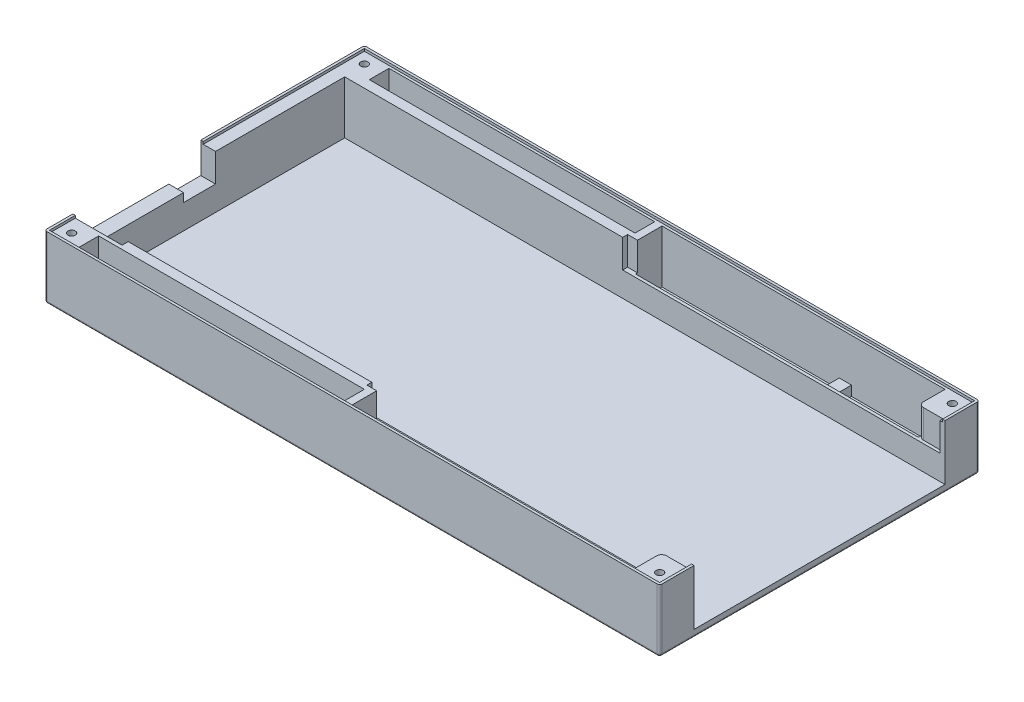
SolidWorks part; units mm, degrees
ref_plane "Front Plane" through (0, 0, 0) normal (0, 0, 1) x (1, 0, 0)
ref_plane "Top Plane" through (0, 0, 0) normal (0, 1, 0) x (1, 0, 0)
ref_plane "Right Plane" through (0, 0, 0) normal (1, 0, 0) x (0, 0, -1)
sketch "Sketch1" plane through (0, 0, 0) normal (0, 1, 0) x (1, 0, 0)
  line L1 (-125, -65) -> (125, -65)
  line L2 (-125, -65) -> (-125, 65)
  line L3 (-125, 65) -> (125, 65)
  line L4 (125, -65) -> (125, 65)
  line L5 (-125, -65) -> (125, 65) construction
  line L6 (-125, 65) -> (125, -65) construction
  point P0 (0, 0)
extrude "Boss-Extrude1" add sketch "Sketch1" along normal blind 3
sketch "Sketch2" plane through (0, 0, 0) normal (0, 1, 0) x (1, 0, 0)
  line L0 (125, -65) -> (125, 65) construction
  line L1 (-125, 65) -> (125, 65)
  line L2 (-125, 65) -> (-125, 64)
  line L3 (-125, 64) -> (125, 64)
  line L4 (125, 65) -> (125, 64)
  dimension "D1" = 1
extrude "Boss-Extrude2" add sketch "Sketch2" along normal blind 25.5
sketch "Sketch3" plane through (0, 3, 0) normal (0, 1, 0) x (1, 0, 0)
  line L0 (125, -65) -> (125, 64) construction
  line L1 (-125, -65) -> (125, -65)
  line L2 (-125, -65) -> (-125, -64)
  line L3 (-125, -64) -> (125, -64)
  line L4 (125, -65) -> (125, -64)
  dimension "D1" = 1
extrude "Boss-Extrude3" add sketch "Sketch3" along normal blind 22.5
sketch "Sketch4" plane through (0, 3, 0) normal (0, 1, 0) x (1, 0, 0)
  line L0 (125, -64) -> (-125, -64) construction
  line L1 (-125, 64) -> (-124, 64)
  line L2 (-125, 64) -> (-125, -64)
  line L3 (-125, -64) -> (-124, -64)
  line L4 (-124, 64) -> (-124, -64)
  dimension "D1" = 1
extrude "Boss-Extrude4" add sketch "Sketch4" along normal blind 22.5
sketch "Sketch6" plane through (0, 3, 0) normal (0, 1, 0) x (1, 0, 0)
  line L1 (125, -65) -> (124, -65)
  line L2 (125, -65) -> (125, -51)
  line L3 (125, -51) -> (124, -51)
  line L4 (124, -65) -> (124, -51)
  dimension "D1" = 1
  dimension "D2" = 14
extrude "Boss-Extrude5" add sketch "Sketch6" along normal blind 22.5
sketch "Sketch7" plane through (0, 3, 0) normal (0, 1, 0) x (1, 0, 0)
  line L1 (125, 65) -> (124, 65)
  line L2 (125, 65) -> (125, 51)
  line L3 (125, 51) -> (124, 51)
  line L4 (124, 65) -> (124, 51)
  dimension "D1" = 1
  dimension "D2" = 14
extrude "Boss-Extrude6" add sketch "Sketch7" along normal blind 22.5
sketch "Sketch8" plane through (0, 3, 0) normal (0, 1, 0) x (1, 0, 0)
  line L0 (-124, 64) -> (124, 64) construction
  line L1 (124, 51) -> (123, 51)
  line L2 (124, 51) -> (124, 64)
  line L3 (124, 64) -> (123, 64)
  line L4 (123, 51) -> (123, 64)
  dimension "D1" = 1
extrude "Boss-Extrude7" add sketch "Sketch8" along normal blind 21.5
sketch "Sketch10" plane through (0, 3, 0) normal (0, 1, 0) x (1, 0, 0)
  line L0 (-124, -64) -> (-124, 64) construction
  line L1 (123, 64) -> (-124, 64)
  line L2 (123, 64) -> (123, 63)
  line L3 (123, 63) -> (-124, 63)
  line L4 (-124, 64) -> (-124, 63)
  dimension "D1" = 1
extrude "Boss-Extrude8" add sketch "Sketch10" along normal blind 21.5
sketch "Sketch11" plane through (0, 3, 0) normal (0, 1, 0) x (1, 0, 0)
  line L0 (124, -64) -> (-124, -64) construction
  line L1 (-124, 63) -> (-123, 63)
  line L2 (-124, 63) -> (-124, -64)
  line L3 (-124, -64) -> (-123, -64)
  line L4 (-123, 63) -> (-123, -64)
  dimension "D1" = 1
extrude "Boss-Extrude9" add sketch "Sketch11" along normal blind 21.5
sketch "Sketch14" plane through (0, 3, 0) normal (0, 1, 0) x (1, 0, 0)
  line L0 (124, -51) -> (124, -64) construction
  line L1 (-123, -64) -> (124, -64)
  line L2 (-123, -64) -> (-123, -63)
  line L3 (-123, -63) -> (124, -63)
  line L4 (124, -64) -> (124, -63)
  dimension "D1" = 1
extrude "Boss-Extrude10" add sketch "Sketch14" along normal blind 21.5
sketch "Sketch15" plane through (0, 3, 0) normal (0, 1, 0) x (1, 0, 0)
  line L1 (124, -63) -> (123, -63)
  line L2 (124, -63) -> (124, -51)
  line L3 (124, -51) -> (123, -51)
  line L4 (123, -63) -> (123, -51)
  dimension "D1" = 1
extrude "Boss-Extrude11" add sketch "Sketch15" along normal blind 21.5
fillet "Fillet1" radius 1 8 edges at (0, 0, -65) (-125, 12.75, -65) (-125, 0, 0) (-125, 12.75, 65) (125, 12.75, -65) (125, 12.75, 65) (0, 0, 65) (125, 0, 0)
sketch "Sketch17" plane through (0, 3, 0) normal (0, 1, 0) x (1, 0, 0)
  line L1 (123, 51) -> (-5, 51)
  line L2 (123, 51) -> (123, 52.2)
  line L3 (123, 52.2) -> (-5, 52.2)
  line L4 (-5, 51) -> (-5, 52.2)
  dimension "D1" = 1.2
  dimension "D2" = 128
extrude "Boss-Extrude12" add sketch "Sketch17" along normal blind 10
sketch "Sketch19" plane through (0, 3, 0) normal (0, 1, 0) x (1, 0, 0)
  line L1 (123, -51) -> (-5, -51)
  line L2 (123, -51) -> (123, -52.2)
  line L3 (123, -52.2) -> (-5, -52.2)
  line L4 (-5, -51) -> (-5, -52.2)
  dimension "D1" = 1.2
  dimension "D2" = 128
extrude "Boss-Extrude13" add sketch "Sketch19" along normal blind 10
sketch "Sketch22" plane through (0, 3, 0) normal (0, 1, 0) x (1, 0, 0)
  line L0 (123, -63) -> (-123, -63) construction
  line L1 (-5, -52.2) -> (-2, -52.2)
  line L2 (-5, -52.2) -> (-5, -63)
  line L3 (-5, -63) -> (-2, -63)
  line L4 (-2, -52.2) -> (-2, -63)
  dimension "D1" = 3
extrude "Boss-Extrude14" add sketch "Sketch22" along normal blind 21.5
sketch "Sketch24" plane through (0, 3, 0) normal (0, 1, 0) x (1, 0, 0)
  line L0 (-123, 63) -> (123, 63) construction
  line L1 (-5, 52.2) -> (-2, 52.2)
  line L2 (-5, 52.2) -> (-5, 63)
  line L3 (-5, 63) -> (-2, 63)
  line L4 (-2, 52.2) -> (-2, 63)
  dimension "D1" = 3
extrude "Boss-Extrude15" add sketch "Sketch24" along normal blind 21.5
sketch "Sketch31" plane through (0, 3, 0) normal (0, 1, 0) x (1, 0, 0)
  line L0 (123, -63) -> (-2, -63) construction
  line L1 (75, -63) -> (70, -63)
  line L2 (75, -63) -> (75, -52.2)
  line L3 (75, -52.2) -> (70, -52.2)
  line L4 (70, -63) -> (70, -52.2)
  line L5 (-2, -52.2) -> (123, -52.2) construction
  dimension "D1" = 5
  dimension "D2" = 48
extrude "Boss-Extrude16" add sketch "Sketch31" along normal blind 4
sketch "Sketch33" plane through (0, 3, 0) normal (0, 1, 0) x (1, 0, 0)
  line L0 (-2, 63) -> (123, 63) construction
  line L1 (75, 63) -> (70, 63)
  line L2 (75, 63) -> (75, 52.2)
  line L3 (75, 52.2) -> (70, 52.2)
  line L4 (70, 63) -> (70, 52.2)
  line L5 (123, 52.2) -> (-2, 52.2) construction
  dimension "D1" = 5
  dimension "D2" = 48
extrude "Boss-Extrude18" add sketch "Sketch33" along normal blind 4
sketch "Sketch44" plane through (0, 3, 0) normal (0, 1, 0) x (1, 0, 0)
  line L0 (-123, -63) -> (-123, 63) construction
  line L1 (-5, -51) -> (-123, -51)
  line L2 (-5, -51) -> (-5, -55)
  line L3 (-5, -55) -> (-123, -55)
  line L4 (-123, -51) -> (-123, -55)
  dimension "D1" = 4
extrude "Boss-Extrude28" add sketch "Sketch44" along normal blind 21.5
sketch "Sketch45" plane through (0, 3, 0) normal (0, 1, 0) x (1, 0, 0)
  line L1 (-123, 63) -> (-113, 63)
  line L2 (-123, 63) -> (-123, 51)
  line L3 (-123, 51) -> (-113, 51)
  line L4 (-113, 63) -> (-113, 51)
  line L5 (-125, 64) -> (-125, -64) construction
  dimension "D1" = 12
  dimension "D2" = 12
extrude "Boss-Extrude29" add sketch "Sketch45" along normal blind 21.5
sketch "Sketch46" plane through (0, 3, 0) normal (0, 1, 0) x (1, 0, 0)
  line L0 (-5, -63) -> (-123, -63) construction
  line L1 (-123, -55) -> (-113, -55)
  line L2 (-123, -55) -> (-123, -63)
  line L3 (-123, -63) -> (-113, -63)
  line L4 (-113, -55) -> (-113, -63)
  dimension "D1" = 10
extrude "Boss-Extrude30" add sketch "Sketch46" along normal blind 21.5
sketch "Sketch47" plane through (0, 3, 0) normal (0, 1, 0) x (1, 0, 0)
  line L0 (123, 52.2) -> (75, 52.2) construction
  line L1 (123, 63) -> (113, 63)
  line L2 (123, 63) -> (123, 52.2)
  line L3 (123, 52.2) -> (113, 52.2)
  line L4 (113, 63) -> (113, 52.2)
  dimension "D1" = 10
extrude "Boss-Extrude31" add sketch "Sketch47" along normal blind 21.5
sketch "Sketch48" plane through (0, 3, 0) normal (0, 1, 0) x (1, 0, 0)
  line L0 (75, -52.2) -> (123, -52.2) construction
  line L1 (123, -63) -> (113, -63)
  line L2 (123, -63) -> (123, -52.2)
  line L3 (123, -52.2) -> (113, -52.2)
  line L4 (113, -63) -> (113, -52.2)
  dimension "D1" = 10
extrude "Boss-Extrude32" add sketch "Sketch48" along normal blind 21.5
sketch "Sketch49" plane through (0, 3, 0) normal (0, 1, 0) x (1, 0, 0)
  line L0 (-113, 51) -> (-113, 63) construction
  line L1 (-5, 51) -> (-113, 51)
  line L2 (-5, 51) -> (-5, 55)
  line L3 (-5, 55) -> (-113, 55)
  line L4 (-113, 51) -> (-113, 55)
  dimension "D1" = 4
extrude "Boss-Extrude33" add sketch "Sketch49" along normal blind 21.5
sketch "Sketch62" plane through (0, 24.5, 0) normal (0, 1, 0) x (1, 0, 0)
  line L0 (124, 65) -> (-124, 65) construction
  line L1 (-125, 64) -> (-125, -64) construction
  circle A0 centre (-119.5, 59.5) radius 1.5
  dimension "D1" = 5.5
  dimension "D2" = 5.5
extrude "CaseMuntHole001" cut sketch "Sketch62" against normal offset from surface (18 mm away) 18 up to face at (-59, 24.5, -59)
sketch "Sketch63" plane through (0, 24.5, 0) normal (0, 1, 0) x (1, 0, 0)
  line L0 (125, 51) -> (125, 64) construction
  line L1 (124, 65) -> (-124, 65) construction
  circle A0 centre (119.5, 59.5) radius 1.5
  dimension "D1" = 5.5
  dimension "D2" = 5.5
extrude "CaseMuntHole002" cut sketch "Sketch63" against normal offset from surface (18 mm away) 18 up to face at (-119.5, 24.5, -58)
sketch "Sketch64" plane through (0, 24.5, 0) normal (0, 1, 0) x (1, 0, 0)
  line L0 (125, -64) -> (125, -51) construction
  line L1 (-124, -65) -> (124, -65) construction
  circle A0 centre (119.5, -59.5) radius 1.5
  dimension "D1" = 5.5
  dimension "D2" = 5.5
extrude "CaseMuntHole003" cut sketch "Sketch64" against normal offset from surface (18 mm away) 18 up to face at (119.5, 24.5, -58)
sketch "Sketch65" plane through (0, 24.5, 0) normal (0, 1, 0) x (1, 0, 0)
  line L0 (-124, -65) -> (124, -65) construction
  line L1 (-125, 64) -> (-125, -64) construction
  circle A0 centre (-119.5, -59.5) radius 1.5
  dimension "D1" = 5.5
  dimension "D2" = 5.5
extrude "CaseMuntHole004" cut sketch "Sketch65" against normal offset from surface (18 mm away) 18 up to face at (119.5, 24.5, 61)
sketch "Sketch67" plane through (0, 3, 0) normal (0, 1, 0) x (1, 0, 0)
  line L1 (-123, 51) -> (-119, 51)
  line L2 (-123, 51) -> (-123, -51)
  line L3 (-123, -51) -> (-119, -51)
  line L4 (-119, 51) -> (-119, -51)
  line L5 (-123, 51) -> (-119, -51) construction
  line L6 (-123, -51) -> (-119, 51) construction
  point P4 (-121, 0)
  dimension "D1" = 4
  dimension "D2" = 102
extrude "Boss-Extrude35" add sketch "Sketch67" along normal blind 21.5
sketch "Sketch72" plane through (-125, 0, 0) normal (-1, 0, 0) x (0, 0, 1)
  line L0 (-64, 25.5) -> (64, 25.5) construction
  line L1 (53.5, 25.5) -> (14.5, 25.5)
  line L2 (53.5, 25.5) -> (53.5, 16.5)
  line L3 (53.5, 16.5) -> (14.5, 16.5)
  line L4 (14.5, 25.5) -> (14.5, 16.5)
  line L5 (53.5, 25.5) -> (14.5, 16.5) construction
  line L6 (53.5, 16.5) -> (14.5, 25.5) construction
  line L7 (65, 25.5) -> (65, 1) construction
  point P4 (34, 21)
  dimension "D1" = 11.5
  dimension "D2" = 9
  dimension "D3" = 39
extrude "Cut-Extrude1" cut sketch "Sketch72" against normal offset from surface (20 mm away) 20 up to face at (-125, 13.25, 0)
sketch "Sketch73" plane through (-125, 0, 0) normal (-1, 0, 0) x (0, 0, 1)
  line L1 (14.5, 25.5) -> (1.5, 25.5)
  line L2 (14.5, 25.5) -> (14.5, 13)
  line L3 (14.5, 13) -> (1.5, 13)
  line L4 (1.5, 25.5) -> (1.5, 13)
  line L5 (14.5, 25.5) -> (1.5, 13) construction
  line L6 (14.5, 13) -> (1.5, 25.5) construction
  point P5 (8, 19.25)
  dimension "D1" = 13
  dimension "D2" = 12.5
extrude "Cut-Extrude2" cut sketch "Sketch73" against normal offset from surface (20 mm away) 20 up to face at (-125, 17.125, 17)
sketch "Sketch74" plane through (0, 24.5, 0) normal (0, 1, 0) x (1, 0, 0)
  line L0 (-2, -63) -> (-2, -52.2) construction
  line L1 (-2, -53) -> (-6, -53)
  line L2 (-2, -53) -> (-2, -51)
  line L3 (-2, -51) -> (-6, -51)
  line L4 (-6, -53) -> (-6, -51)
  line L5 (-2, -53) -> (-6, -51) construction
  line L6 (-2, -51) -> (-6, -53) construction
  line L7 (-5, -51) -> (-105, -51) construction
  point P4 (-4, -52)
  dimension "D1" = 4
  dimension "D2" = 2
extrude "Cut-Extrude3" cut sketch "Sketch74" against normal blind 11.5
sketch "Sketch75" plane through (0, 24.5, 0) normal (0, 1, 0) x (1, 0, 0)
  line L0 (-119, 51) -> (-5, 51) construction
  line L1 (-6, 51) -> (-2, 51)
  line L2 (-6, 51) -> (-6, 53)
  line L3 (-6, 53) -> (-2, 53)
  line L4 (-2, 51) -> (-2, 53)
  line L5 (-6, 51) -> (-2, 53) construction
  line L6 (-6, 53) -> (-2, 51) construction
  line L7 (-2, 52.2) -> (-2, 63) construction
  point P4 (-4, 52)
  dimension "D1" = 4
  dimension "D2" = 2
extrude "Cut-Extrude4" cut sketch "Sketch75" against normal blind 11.5
fillet "Fillet2" radius 2 2 edges at (113, 18.75, -52.2) (113, 18.75, 52.2)
